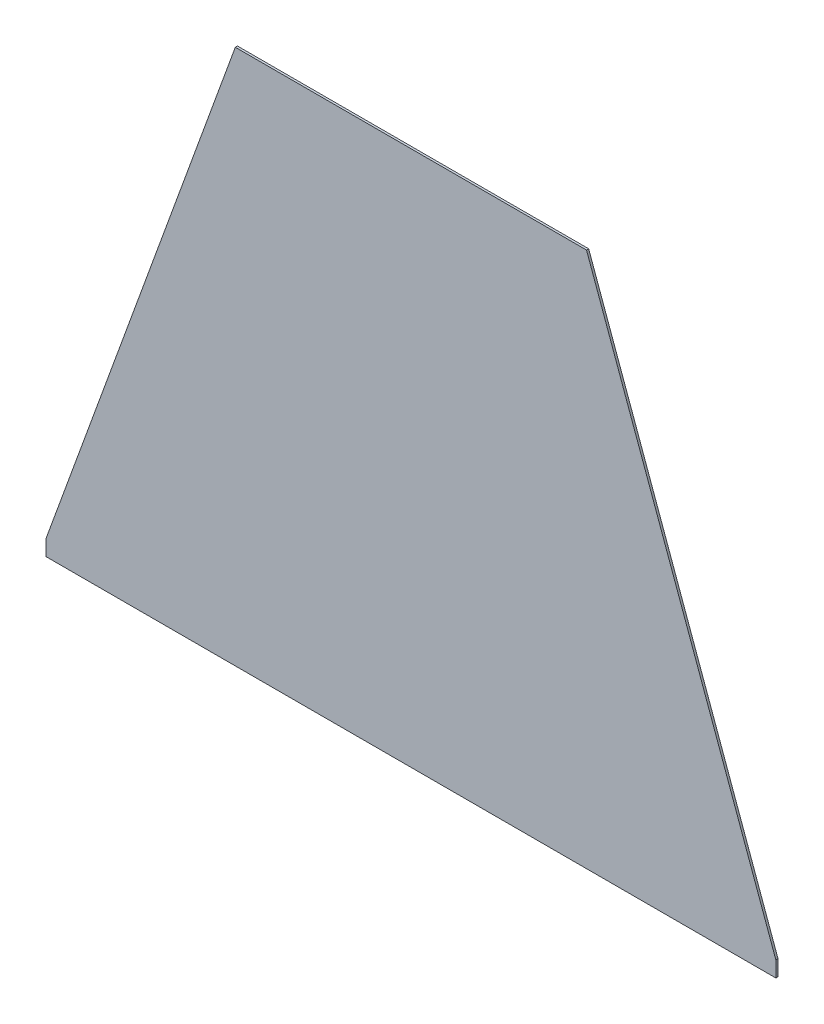
SolidWorks part; units mm, degrees
ref_plane "Alzado" through (0, 0, 0) normal (0, 0, 1) x (1, 0, 0)
ref_plane "Planta" through (0, 0, 0) normal (0, 1, 0) x (1, 0, 0)
ref_plane "Vista lateral" through (0, 0, 0) normal (1, 0, 0) x (0, 0, -1)
sketch "Croquis1" plane through (0, 0, 0) normal (0, 0, 1) x (1, 0, 0)
  line L0 (0, 0) -> (650, 0)
  line L1 (0, 0) -> (171.0101, 469.8463)
  line L2 (650, 0) -> (478.9899, 469.8463)
  line L3 (171.0101, 469.8463) -> (478.9899, 469.8463)
  dimension "D1" = 650
  dimension "D2" = 70
  dimension "D3" = 500
  dimension "D4" = 70
extrude "Saliente-Extruir1" add sketch "Croquis1" along normal blind 1.9
sketch "Croquis2" plane through (0, 0, 1.9) normal (0, 0, 1) x (1, 0, 0)
  line L1 (650, 0) -> (645, 0)
  line L2 (650, 0) -> (650, 30.8277)
  line L3 (650, 30.8277) -> (645, 30.8277)
  line L4 (645, 0) -> (645, 30.8277)
  line L5 (0, 0) -> (5, 0)
  line L6 (0, 0) -> (0, 21.5727)
  line L7 (0, 21.5727) -> (5, 21.5727)
  line L8 (5, 0) -> (5, 21.5727)
  dimension "D1" = 5
  dimension "D2" = 5
extrude "Cortar-Extruir1" cut sketch "Croquis2" against normal blind 10
